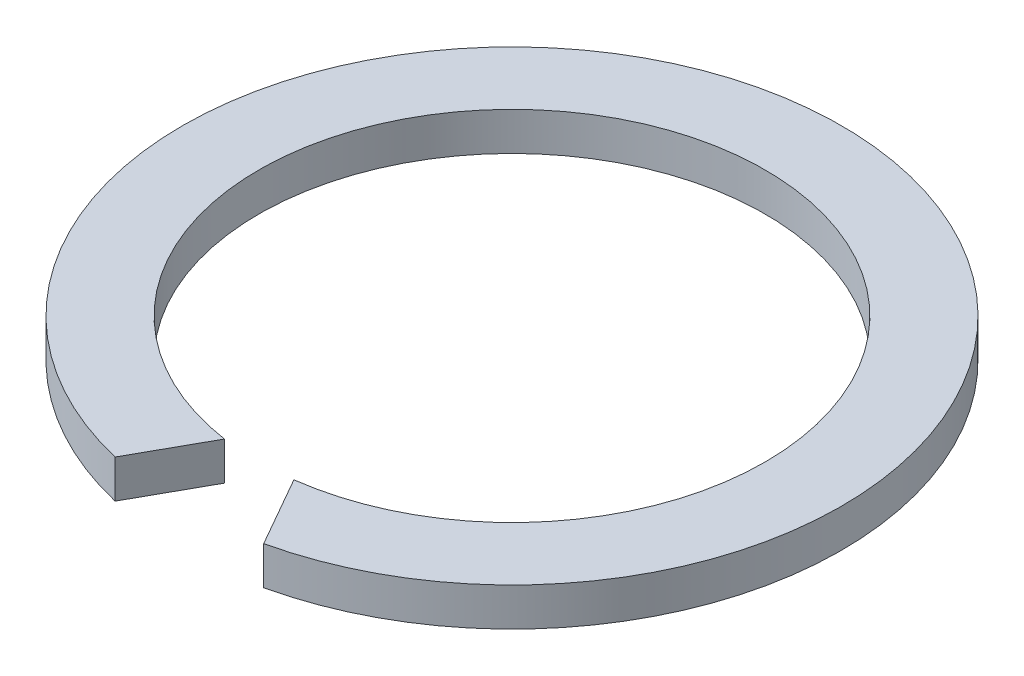
SolidWorks part; units mm, degrees
ref_plane "Front Plane" through (0, 0, 0) normal (0, 0, 1) x (1, 0, 0)
ref_plane "Top Plane" through (0, 0, 0) normal (0, 1, 0) x (1, 0, 0)
ref_plane "Right Plane" through (0, 0, 0) normal (1, 0, 0) x (0, 0, -1)
sketch "Sketch1" plane through (0, 0, 0) normal (0, 1, 0) x (1, 0, 0)
  circle A0 centre (0, 0) radius 16.55
  circle A1 centre (0, 0) radius 21.55
extrude "Boss-Extrude1" add sketch "Sketch1" along normal blind 2.5
sketch "Sketch3" plane through (0, 0, 0) normal (0, 1, 0) x (1, 0, 0)
  line L0 (0, 0) -> (0, -27.1481) construction
  line L1 (-6.052, -22.8814) -> (5.8428, -22.8814)
  line L2 (0, -15.6377) -> (-2.0251, -15.6377)
  line L3 (0, -15.6377) -> (1.7076, -15.6377)
  line L4 (1.7076, -15.6377) -> (5.8428, -22.8814)
  line L5 (-6.052, -22.8814) -> (-2.0251, -15.6377)
  point P7 (-5.9068, -22.6818)
  point P9 (5.8428, -22.8814)
  point P10 (-2.0568, -15.6947)
  point P11 (1.7076, -15.6377)
extrude "Cut-Extrude2" cut sketch "Sketch3" against normal blind 12 and the other way blind 15
